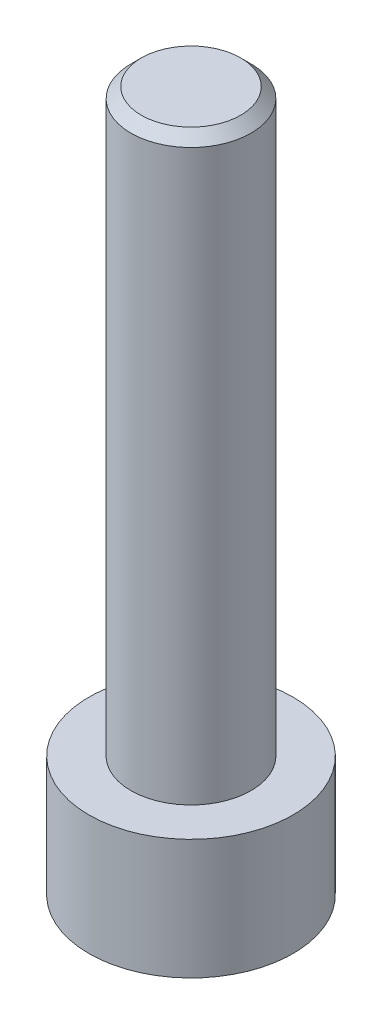
SolidWorks part; units mm, degrees
material "201 Annealed Stainless Steel (SS)"
ref_plane "Front Plane" through (0, 0, 0) normal (0, 0, 1) x (1, 0, 0)
ref_plane "Top Plane" through (0, 0, 0) normal (0, 1, 0) x (1, 0, 0)
ref_plane "Right Plane" through (0, 0, 0) normal (1, 0, 0) x (0, 0, -1)
sketch "Sketch1" plane through (0, 0, 0) normal (0, 1, 0) x (1, 0, 0)
  circle A0 centre (0, 0) radius 2.465
  dimension "D1" = 4.93
extrude "Boss-Extrude1" add sketch "Sketch1" along normal blind 2.9
sketch "Sketch2" plane through (0, 2.9, 0) normal (0, 1, 0) x (1, 0, 0)
  circle A0 centre (0, 0) radius 1.45
  dimension "D1" = 2.9
extrude "Boss-Extrude2" add sketch "Sketch2" along normal blind 14
sketch "Sketch3" plane through (0, 0, 0) normal (0, -1, 0) x (1, 0, 0)
  line L1 (0.7332, -1.27) -> (1.4665, 0)
  line L2 (1.4665, 0) -> (0.7332, 1.27)
  line L3 (0.7332, 1.27) -> (-0.7332, 1.27)
  line L4 (-0.7332, 1.27) -> (-1.4665, 0)
  line L5 (-1.4665, 0) -> (-0.7332, -1.27)
  line L6 (-0.7332, -1.27) -> (0.7332, -1.27)
  circle A0 centre (0, 0) radius 1.27 construction
  dimension "D1" = 2.54
extrude "Cut-Extrude1" cut sketch "Sketch3" against normal blind 1.9
chamfer "Chamfer1" distance 0.25 angle 45 1 edges at (0, 16.9, 1.45)
